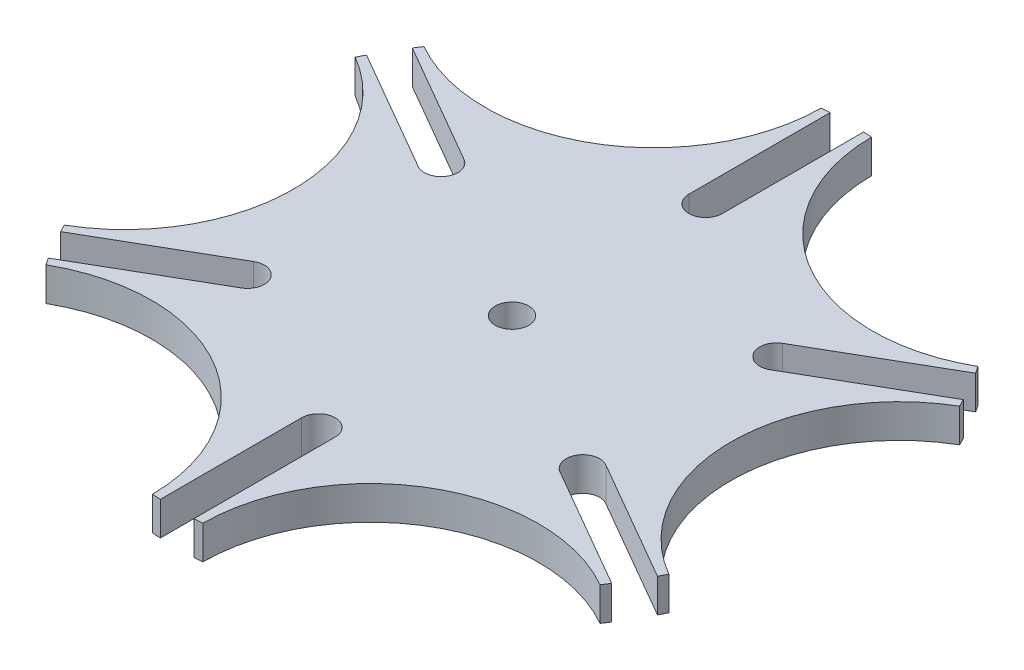
SolidWorks part; units mm, degrees
ref_plane "Front Plane" through (0, 0, 0) normal (0, 0, 1) x (1, 0, 0)
ref_plane "Top Plane" through (0, 0, 0) normal (0, 1, 0) x (1, 0, 0)
ref_plane "Right Plane" through (0, 0, 0) normal (1, 0, 0) x (0, 0, -1)
sketch "Sketch1" plane through (0, 0, 0) normal (0, 1, 0) x (1, 0, 0)
  line L0 (0, 50) -> (0, 0) construction
  line L1 (0, 50) -> (0, 57.735) construction
  line L2 (5, 99.8749) -> (5, 57.735)
  line L3 (-5, 99.8749) -> (-5, 57.735)
  line L4 (83.9942, 54.2676) -> (47.5, 33.1976)
  line L5 (88.9942, 45.6073) -> (52.5, 24.5374)
  line L6 (88.9942, -45.6073) -> (52.5, -24.5374)
  line L7 (83.9942, -54.2676) -> (47.5, -33.1976)
  line L8 (5, -99.8749) -> (5, -57.735)
  line L9 (-5, -99.8749) -> (-5, -57.735)
  line L10 (-83.9942, -54.2676) -> (-47.5, -33.1976)
  line L11 (-88.9942, -45.6073) -> (-52.5, -24.5374)
  line L12 (-88.9942, 45.6073) -> (-52.5, 24.5374)
  line L13 (-83.9942, 54.2676) -> (-47.5, 33.1976)
  line L14 (0, 0) -> (115.4701, 0) construction
  line L15 (0, 0) -> (86.6025, 50) construction
  line L16 (86.6025, 50) -> (90.3525, 43.5048) construction
  arc A0 (-5, 99.8749) -> (-7.5008, 99.7183) centre (0, 0) ccw
  arc A1 (47.5, 33.1976) -> (52.5, 24.5374) centre (50, 28.8675) ccw
  arc A2 (-5, 57.735) -> (5, 57.735) centre (0, 57.735) ccw
  arc A3 (52.5, -24.5374) -> (47.5, -33.1976) centre (50, -28.8675) ccw
  arc A4 (5, -57.735) -> (-5, -57.735) centre (0, -57.735) ccw
  arc A5 (-47.5, -33.1976) -> (-52.5, -24.5374) centre (-50, -28.8675) ccw
  arc A6 (-52.5, 24.5374) -> (-47.5, 33.1976) centre (-50, 28.8675) ccw
  arc A7 (-88.9942, 45.6073) -> (-90.109, 43.3633) centre (0, 0) ccw
  arc A8 (-83.9942, -54.2676) -> (-82.6082, -56.355) centre (0, 0) ccw
  arc A9 (5, -99.8749) -> (7.5008, -99.7183) centre (0, 0) ccw
  arc A10 (88.9942, -45.6073) -> (90.109, -43.3633) centre (0, 0) ccw
  arc A11 (83.9942, 54.2676) -> (82.6082, 56.355) centre (0, 0) ccw
  arc A12 (90.3525, 43.5048) -> (90.109, -43.3633) centre (115.4701, 0) ccw
  arc A13 (90.109, 43.3633) -> (88.9942, 45.6073) centre (0, 0) ccw
  arc A14 (82.6082, -56.355) -> (7.5008, -99.7183) centre (57.735, -100) ccw
  arc A15 (-7.5008, -99.7183) -> (-82.6082, -56.355) centre (-57.735, -100) ccw
  arc A16 (-90.109, -43.3633) -> (-90.109, 43.3633) centre (-115.4701, 0) ccw
  arc A17 (-82.6082, 56.355) -> (-7.5008, 99.7183) centre (-57.735, 100) ccw
  arc A18 (7.5008, 99.7183) -> (82.6082, 56.355) centre (57.735, 100) ccw
  arc A19 (-82.6082, 56.355) -> (-83.9942, 54.2676) centre (0, 0) ccw
  arc A20 (7.5008, 99.7183) -> (5, 99.8749) centre (0, 0) ccw
  arc A21 (-90.109, -43.3633) -> (-88.9942, -45.6073) centre (0, 0) ccw
  arc A22 (-7.5008, -99.7183) -> (-5, -99.8749) centre (0, 0) ccw
  arc A23 (82.6082, -56.355) -> (83.9942, -54.2676) centre (0, 0) ccw
  circle A24 centre (0, 0) radius 5
  point P4 (0, 35.952)
  point P37 (0, 0)
  point P58 (0, 0)
extrude "Boss-Extrude1" add sketch "Sketch1" along normal blind 10 contours A14 A23 L7 A3 L6 A10 A12 A13 L5 A1 L4 A11 A18 A20 L2 A2 L3 A0 A17 A19 L13 A6 L12 A7 A16 A21 L11 A5 L10 A8 A15 A22 L9 A4 L8 A9
equation "\"b\"=100"
equation "\"D1@Sketch1\"=\"b\"*2"
equation "\"p\"=5"
equation "\"D2@Sketch1\"=\"p\""
equation "\"c\"= \"b\" / cos ( 180 / 6 )"
equation "\"D4@Sketch1\"=\"b\"/cos(180/6)"
equation "\"D6@Sketch1\"=\"b\""
equation "\"a\"= ( \"c\" ^ 2 - \"b\" ^ 2 ) ^ .5"
equation "\"s\"= \"a\" + \"b\" - \"c\""
equation "\"y\"= \"a\" - ( \"p\" * 1.5 )"
equation "\"D5@Sketch1\"=\"s\""
equation "\"D7@Sketch1\"=\"y\"*2"
equation "\"D13@Sketch1\"=\"p\"*2"
